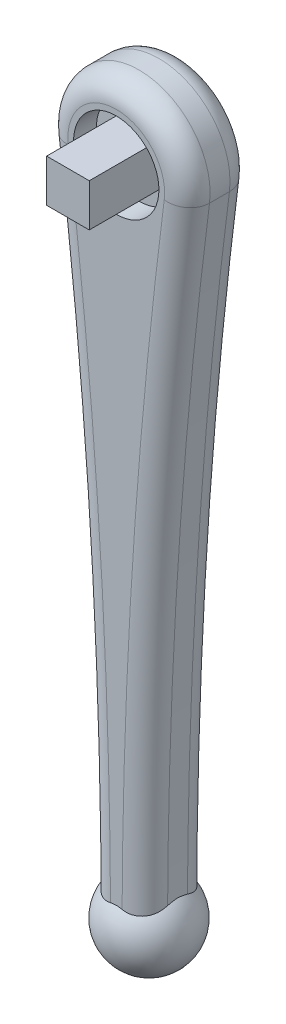
SolidWorks part; units mm, degrees
ref_plane "Front Plane" through (0, 0, 0) normal (0, 0, 1) x (1, 0, 0)
ref_plane "Top Plane" through (0, 0, 0) normal (0, 1, 0) x (1, 0, 0)
ref_plane "Right Plane" through (0, 0, 0) normal (1, 0, 0) x (0, 0, -1)
sketch "Sketch3" plane through (0, 0, 0) normal (0, 0, 1) x (1, 0, 0)
  circle A0 centre (0, 0) radius 15
  circle A1 centre (0, 0) radius 25
  dimension "D1" = 30
  dimension "D2" = 50
extrude "Boss-Extrude1" add sketch "Sketch3" along normal blind 8
sketch "Sketch4" plane through (0, 0, 0) normal (0, 0, -1) x (-1, 0, 0)
  circle A0 centre (0, 0) radius 25 construction
  circle A1 centre (0, 0) radius 25
extrude "Boss-Extrude2" add sketch "Sketch4" along normal blind 15
sketch "Sketch5" plane through (0, 0, 0) normal (0, 0, 1) x (1, 0, 0)
  line L1 (-7.5, -7.5) -> (7.5, -7.5)
  line L2 (-7.5, -7.5) -> (-7.5, 7.5)
  line L3 (-7.5, 7.5) -> (7.5, 7.5)
  line L4 (7.5, -7.5) -> (7.5, 7.5)
  line L5 (-7.5, -7.5) -> (7.5, 7.5) construction
  line L6 (-7.5, 7.5) -> (7.5, -7.5) construction
  point P0 (0, 0)
  dimension "D1" = 15
  dimension "D2" = 15
extrude "Boss-Extrude3" add sketch "Sketch5" along normal blind 25
sketch "Sketch6" plane through (0, 0, -15) normal (0, 0, -1) x (-1, 0, 0)
  line L0 (0, 0) -> (0, -235) construction
  line L1 (-25.2074, 0) -> (25, 0) construction
  line L2 (-10, -235) -> (10, -235) construction
  circle A0 centre (0, -235) radius 10
  circle A1 centre (0, 0) radius 25 construction
  arc A2 (-10, -235) -> (-25.2074, 0) centre (-1833.3333, -235) ccw
  arc A3 (10, -235) -> (25.2074, 0) centre (1833.3333, -235) cw
  circle M2 centre (0, 0) radius 25
  dimension "D2" = 20
  dimension "D1" = 235
extrude "Boss-Extrude4" add sketch "Sketch6" against normal up to surface (23 mm away) contours A0 A3 A2 M2 | A0 up to face at (25, 0, 8)
ref_plane "Plane2" through (0, 0, -3.5) normal (0, 0, -1) x (-1, 0, 0)
sketch "Sketch7" plane through (0, 0, -3.5) normal (0, 0, -1) x (-1, 0, 0)
  line L0 (0, -220) -> (0, -250) construction
  circle A0 centre (0, -235) radius 15
  dimension "D1" = 30
revolve "Revolve2" add sketch "Sketch7" angle 360 about L0
fillet "Fillet1" radius 8 4 edges at (-13.703, -118.8534, -15) (0, 25, -15) (13.703, -118.8534, -15) (0, -245, -15)
fillet "Fillet2" radius 8 4 edges at (-13.703, -118.8534, 8) (0, 25, 8) (13.703, -118.8534, 8) (0, -245, 8)
sketch "Sketch8" plane through (0, 0, 0) normal (0, 0, 1) x (1, 0, 0)
  line L0 (7.5, 0) -> (15, 0) construction
  line L1 (7.5, -7.5) -> (7.5, 7.5) construction
  circle A0 centre (0, 0) radius 15 construction
  circle A1 centre (11.25, 0) radius 1.5
  circle A2 centre (0, -11.25) radius 1.5
  circle A3 centre (-11.25, 0) radius 1.5
  circle A4 centre (0, 11.25) radius 1.5
  point P18 (0, 0)
  dimension "D1" = 3
  dimension "D2" = 4
extrude "Cut-Extrude1" cut sketch "Sketch8" against normal through all both and the other way through all
sketch "Sketch9" plane through (0, 0, -15) normal (0, 0, -1) x (-1, 0, 0)
  circle A0 centre (0, 11.25) radius 3.5
  circle A1 centre (11.25, 0) radius 3.5
  circle A2 centre (0, -11.25) radius 3.5
  circle A3 centre (-11.25, 0) radius 3.5
  point P12 (0, 0)
  circle M5 centre (-11.25, 0) radius 1.5
  circle M6 centre (0, -11.25) radius 1.5
  circle M7 centre (11.25, 0) radius 1.5
  dimension "D1" = 7
  dimension "D2" = 4
extrude "Cut-Extrude2" cut sketch "Sketch9" against normal offset from surface (9 mm away) 6 contours A1 M7 | A2 M6 | A3 M5 | A0 up to face at (9.75, 0, 0)
